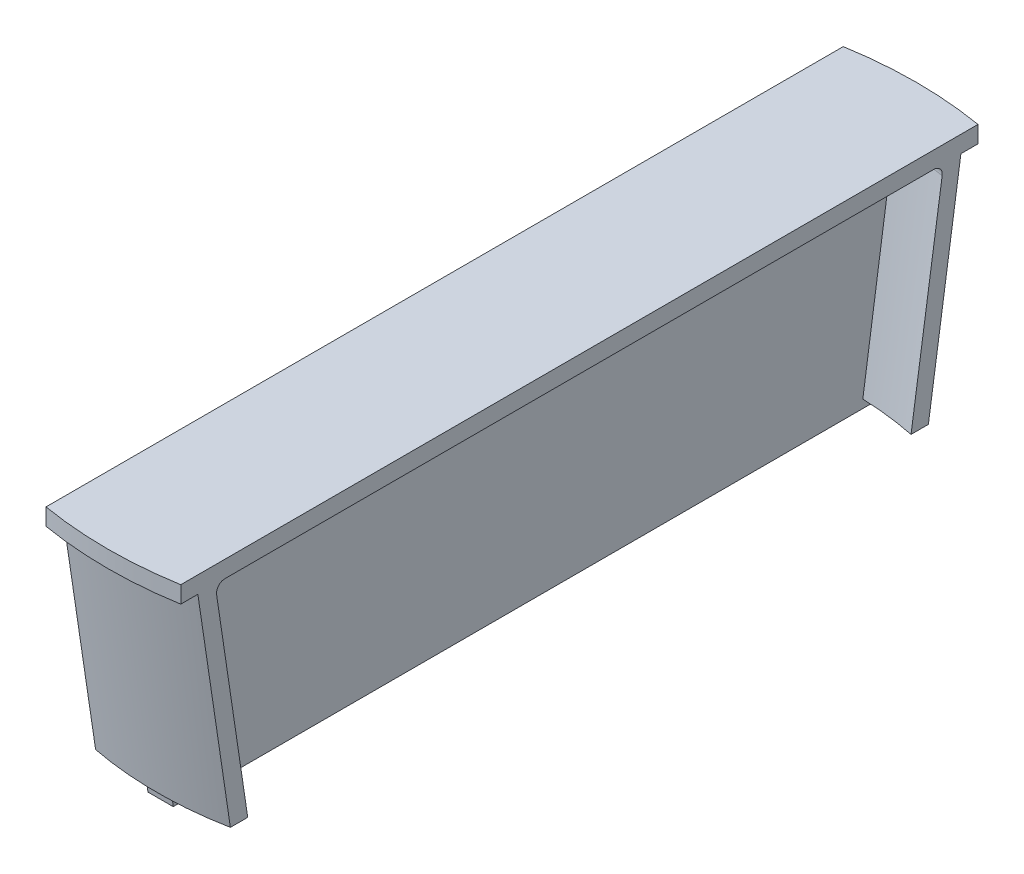
SolidWorks part; units mm, degrees
ref_plane "Front Plane" through (0, 0, 0) normal (0, 0, 1) x (1, 0, 0)
ref_plane "Top Plane" through (0, 0, 0) normal (0, 1, 0) x (1, 0, 0)
ref_plane "Right Plane" through (0, 0, 0) normal (1, 0, 0) x (0, 0, -1)
sketch "Sketch1" plane through (0, 0, 0) normal (0, 0, 1) x (1, 0, 0)
  line L0 (0, 0) -> (0, -35.4403) construction
  line L1 (0, 0) -> (-48, 0)
  line L2 (-48, 0) -> (-48, -2)
  line L3 (-42.8213, -2) -> (0, -2)
  line L4 (-46, 5.1437) -> (-46, -13.8811) construction
  line L5 (-46, -2) -> (-42.2029, -27.9019)
  line L6 (-43.8108, -3.145) -> (-40.1815, -27.9019)
  line L7 (-44.0212, -1.7099) -> (-40.1815, -27.9019) construction
  line L8 (-40.1815, -27.9019) -> (-42.2029, -27.9019)
  line L9 (-46, -2) -> (-42.1603, -28.192) construction
  line L10 (-46, -2) -> (-48, -2)
  line L11 (0, 0) -> (0, -2)
  arc A0 (-42.8213, -2) -> (-43.8108, -3.145) centre (-42.8213, -3) ccw
  dimension "D6" = 1
  dimension "D1" = 48
  dimension "D2" = 2
  dimension "D3" = 2
  dimension "D4" = 81.66
  dimension "D5" = 2
revolve "Revolve1" add sketch "Sketch1" angle 360 about L0
ref_plane "InsideCapPlane" through (0, -2.1, 0) normal (0, -1, 0) x (-1, 0, 0)
sketch "Sketch13" plane through (0, 0, 0) normal (1, 0, 0) x (0, 0, -1)
  line L0 (-45.3415, -0.9316) -> (45.3415, -0.9316)
  line L1 (45.3415, -0.9316) -> (41.3201, -28.8805)
  line L2 (41.3201, -28.8805) -> (-41.7222, -28.8805)
  line L3 (-41.7222, -28.8805) -> (-45.3415, -0.9316)
extrude "Boss-Extrude2" add sketch "Sketch13" along normal mid plane 3
ref_plane "Cut Plane 1" through (8, 0, 0) normal (1, 0, 0) x (0, 0, -1)
ref_plane "Cut Plane 2" through (-8, 0, 0) normal (1, 0, 0) x (0, 0, -1)
sketch "CutPlane1 Sketch" plane through (8, 0, 0) normal (1, 0, 0) x (0, 0, -1)
  line L1 (-61.3769, 14.5894) -> (61.8193, 14.5894)
  line L2 (-61.3769, 14.5894) -> (-61.3769, -38.9357)
  line L3 (-61.3769, -38.9357) -> (61.8193, -38.9357)
  line L4 (61.8193, 14.5894) -> (61.8193, -38.9357)
  line L5 (-61.3769, 14.5894) -> (61.8193, -38.9357) construction
  line L6 (-61.3769, -38.9357) -> (61.8193, 14.5894) construction
  point P4 (0.2212, -12.1732)
sketch "CutPlane2 Sketch" plane through (-8, 0, 0) normal (1, 0, 0) x (0, 0, -1)
  line L1 (-61.3769, 14.5894) -> (61.8193, 14.5894)
  line L2 (-61.3769, 14.5894) -> (-61.3769, -38.9357)
  line L3 (-61.3769, -38.9357) -> (61.8193, -38.9357)
  line L4 (61.8193, 14.5894) -> (61.8193, -38.9357)
  line L5 (-61.3769, 14.5894) -> (61.8193, -38.9357) construction
  line L6 (-61.3769, -38.9357) -> (61.8193, 14.5894) construction
  point P4 (0.2212, -12.1732)
extrude "Cut-Extrude6" cut sketch "CutPlane1 Sketch" along normal blind 111
extrude "Cut-Extrude7" cut sketch "CutPlane2 Sketch" against normal blind 111
